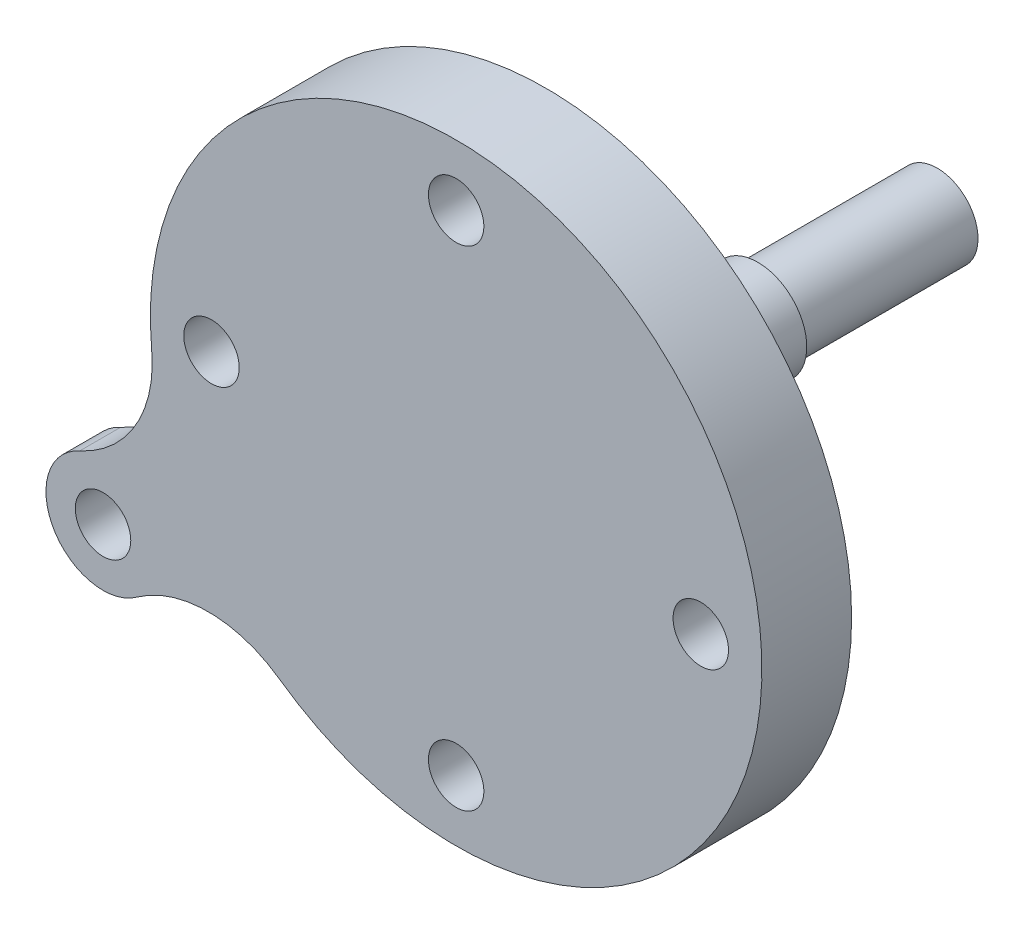
SolidWorks part; units mm, degrees
material "Alumina"
ref_plane "Plan de face" through (0, 0, 0) normal (0, 0, 1) x (1, 0, 0)
ref_plane "Plan de dessus" through (0, 0, 0) normal (0, 1, 0) x (1, 0, 0)
ref_plane "Plan de droite" through (0, 0, 0) normal (1, 0, 0) x (0, 0, -1)
sketch "Sketch1" plane through (0, 0, 0) normal (0, 0, 1) x (1, 0, 0)
  circle A0 centre (0, 0) radius 37.5
  circle A1 centre (0, 0) radius 30 construction
  dimension "D1" = 75
  dimension "D2" = 60
extrude "Boss-Extrude1" add sketch "Sketch1" along normal blind 11
hole_wizard "Tap Drill for M8 Tap1" positions "Sketch7" profile "Sketch8" hole size "M8" standard "ISO"
sketch "Sketch7" plane through (0, 0, 11) normal (0, 0, 1) x (1, 0, 0)
  circle A0 centre (0, 0) radius 30 construction
  point P5 (0, 30)
  point P7 (30, 0)
  point P9 (0, -30)
  point P11 (-30, 0)
  dimension "D1" = 60
sketch "Sketch8" plane through (-30, 0, 11) normal (1, 0, 0) x (0, -1, 0)
  line L0 (0, 0) -> (0, 25.0429)
  line L1 (0, 25.0429) -> (3.4, 23)
  line L2 (3.4, 23) -> (3.4, 0)
  line L5 (3.4, 0) -> (0, 0)
  line L10 (0, 25.0429) -> (-3.4, 23) construction
  line L11 (0, -6.35) -> (0, 107.95) construction
  dimension "Hole Dia." = 6.8
  dimension "Hole Depth" = 23
  dimension "Drill Angle" = 118
sketch "Sketch6" plane through (0, 0, 0) normal (0, 0, -1) x (-1, 0, 0)
  circle A0 centre (0, 0) radius 12
  dimension "D1" = 24
extrude "Boss.-Extru.1" add sketch "Sketch6" along normal blind 1
sketch "Sketch5" plane through (0, 0, -1) normal (0, 0, -1) x (-1, 0, 0)
  circle A0 centre (0, 0) radius 10
  dimension "D1" = 20
extrude "Boss.-Extru.2" add sketch "Sketch5" along normal blind 11
sketch "Esquisse1" plane through (0, 0, -12) normal (0, 0, -1) x (-1, 0, 0)
  circle A0 centre (0, 0) radius 6
  dimension "D1" = 12
extrude "Boss.-Extru.3" add sketch "Esquisse1" along normal blind 14
sketch "Esquisse4" plane through (0, 0, -26) normal (0, 0, -1) x (-1, 0, 0)
  circle A0 centre (0, 0) radius 5
  dimension "D1" = 10
extrude "Boss.-Extru.4" add sketch "Esquisse4" along normal blind 22
hole_wizard "Trou pour taraudage pour trou taraudé M61" positions "Esquisse2" profile "Esquisse3" hole size "M6" standard "ISO"
sketch "Esquisse2" plane through (0, 0, -48) normal (0, 0, -1) x (-1, 0, 0)
  point P0 (0, 0)
sketch "Esquisse3" plane through (0, 0, -48) normal (1, 0, 0) x (0, 1, 0)
  line L0 (0, 0) -> (0, 24.5022)
  line L1 (0, 24.5022) -> (2.5, 23)
  line L2 (2.5, 23) -> (2.5, 0)
  line L5 (2.5, 0) -> (0, 0)
  line L10 (0, 24.5022) -> (-2.5, 23) construction
  line L11 (0, -6.35) -> (0, 107.95) construction
  dimension "Diamètre du perçage" = 5
  dimension "Profondeur du perçage" = 23
  dimension "Angle de pointe" = 118
sketch "Esquisse5" plane through (0, 0, 0) normal (0, 1, 0) x (1, 0, 0)
  line L0 (0, 27.924) -> (0, 48) construction
  line L1 (5, 48) -> (-5, 48) construction
  line L2 (-1.5, 27.924) -> (-1.5, 48)
  line L3 (1.5, 27.924) -> (1.5, 48)
  arc A0 (-1.5, 27.924) -> (1.5, 27.924) centre (0, 27.924) ccw
  arc A1 (1.5, 48) -> (-1.5, 48) centre (0, 48) ccw
  point P4 (0, 37.962)
  dimension "D1" = 1.5
extrude "Enlèv. mat.-Extru.1" cut sketch "Esquisse5" against normal blind 10 from offset 3.2 offset against normal yes
sketch "Esquisse6" plane through (0, 0, 11) normal (0, 0, 1) x (1, 0, 0)
  line L0 (-43.3013, -25) -> (0, 0) construction
  line L1 (0, 0) -> (-37.5, 0) construction
  arc A0 (-46.1549, -18.6081) -> (-39.1925, -30.6673) centre (-43.3013, -25) ccw
  circle A1 centre (0, 0) radius 37.5 construction
  arc A2 (-46.1549, -18.6081) -> (-37.3356, -3.5079) centre (-52.2698, -4.9111) ccw
  circle A3 centre (0, 0) radius 37.5
  arc A4 (-37.3356, -3.5079) -> (-21.7057, -30.5796) centre (0, 0) ccw
  arc A5 (-21.7057, -30.5796) -> (-39.1925, -30.6673) centre (-30.388, -42.8114) ccw
  dimension "D1" = 14
  dimension "D2" = 50
  dimension "D5" = 30
  dimension "D3" = 30
  dimension "D4" = 0
extrude "Boss.-Extru.5" add sketch "Esquisse6" against normal blind 5
hole_wizard "Trou pour taraudage pour trou taraudé M81" positions "Esquisse7" profile "Esquisse8" hole size "M8" standard "ISO"
sketch "Esquisse7" plane through (0, 0, 11) normal (0, 0, 1) x (1, 0, 0)
  point P0 (-43.3013, -25)
sketch "Esquisse8" plane through (-43.3013, -25, 11) normal (1, 0, 0) x (0, -1, 0)
  line L0 (0, 0) -> (0, 10.0429)
  line L1 (0, 10.0429) -> (3.4, 8)
  line L2 (3.4, 8) -> (3.4, 0)
  line L5 (3.4, 0) -> (0, 0)
  line L10 (0, 10.0429) -> (-3.4, 8) construction
  line L11 (0, -6.35) -> (0, 107.95) construction
  dimension "Diamètre du perçage" = 6.8
  dimension "Profondeur du perçage" = 8
  dimension "Angle de pointe" = 118
